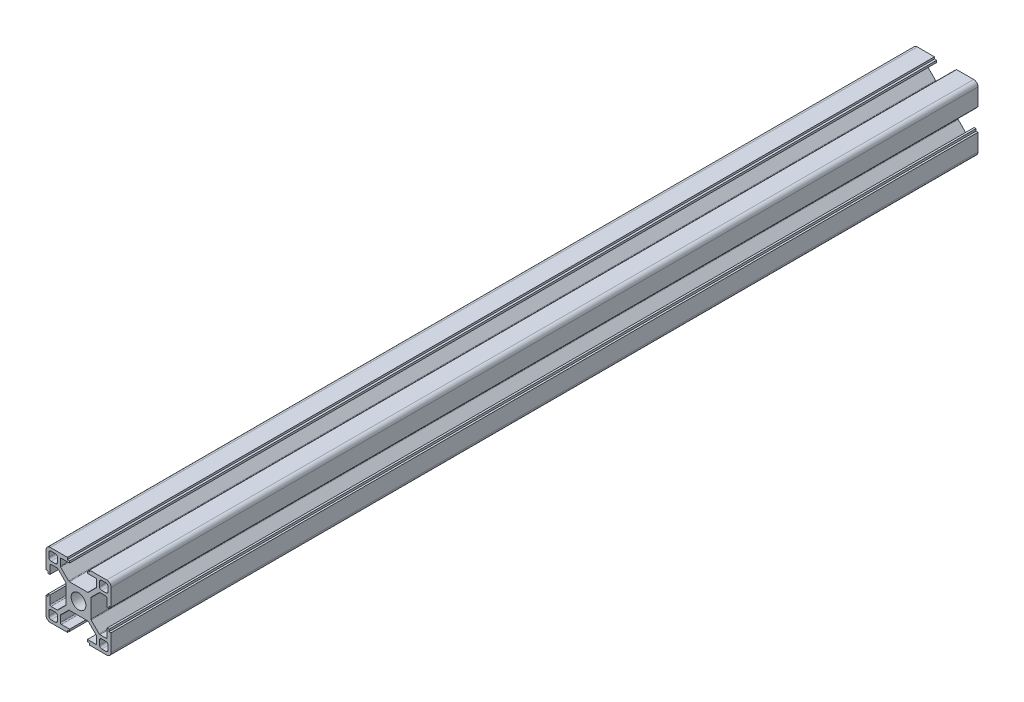
SolidWorks part; units mm, degrees
ref_plane "前视基准面" through (0, 0, 0) normal (0, 0, 1) x (1, 0, 0)
ref_plane "上视基准面" through (0, 0, 0) normal (0, 1, 0) x (1, 0, 0)
ref_plane "右视基准面" through (0, 0, 0) normal (1, 0, 0) x (0, 0, -1)
sketch "草图1" plane through (0, 0, 0) normal (0, 0, 1) x (1, 0, 0)
  line L0 (0, 0) -> (0, 65.3905) construction
  line L1 (0, 0) -> (64.2648, 0) construction
  line L2 (0, 0) -> (79.9729, 79.9729) construction
  line L3 (5.7, 0) -> (5.7, 4.4272)
  line L4 (5.7, 4.4272) -> (9.6728, 8.4)
  line L5 (9.6728, 8.4) -> (13.2, 8.4)
  line L6 (13.2, 8.4) -> (13.2, 4.1)
  line L7 (13.2, 4.1) -> (14.1, 4.1)
  line L8 (14.1, 4.1) -> (14.1, 5.1)
  line L9 (14.1, 5.1) -> (15, 5.1)
  line L10 (15, 5.1) -> (15, 15)
  line L11 (5.1, 15) -> (15, 15)
  line L12 (5.1, 14.1) -> (5.1, 15)
  line L13 (4.1, 14.1) -> (5.1, 14.1)
  line L14 (4.1, 13.2) -> (4.1, 14.1)
  line L15 (8.4, 13.2) -> (4.1, 13.2)
  line L16 (8.4, 9.6728) -> (8.4, 13.2)
  line L17 (4.4272, 5.7) -> (8.4, 9.6728)
  line L18 (0, 5.7) -> (4.4272, 5.7)
  line L20 (9.7, 9.7) -> (13.7, 9.7)
  line L21 (9.7, 9.7) -> (9.7, 13.7)
  line L22 (9.7, 13.7) -> (13.7, 13.7)
  line L23 (13.7, 9.7) -> (13.7, 13.7)
  line L24 (9.7, 9.7) -> (13.7, 13.7) construction
  line L25 (9.7, 13.7) -> (13.7, 9.7) construction
  line L26 (0, 5.7) -> (0, 0)
  line L27 (0, 0) -> (5.7, 0)
  point P9 (11.7, 11.7)
  dimension "D1" = 45
  dimension "D2" = 5.7
  dimension "D3" = 1.8
  dimension "D4" = 0.9
  dimension "D5" = 8.2
  dimension "D6" = 10.2
  dimension "D7" = 1.8
  dimension "D8" = 15
  dimension "D9" = 16.8
  dimension "D10" = 4
  dimension "D11" = 1.3
extrude "凸台-拉伸1" add sketch "草图1" along normal blind 400 contours L3 L4 L5 L6 L7 L8 L9 L10 L11 L12 L13 L14 L15 L16 L17 L18 L26 L27
fillet "圆角1" radius 1 4 edges at (9.7, 9.7, 200) (13.7, 9.7, 200) (9.7, 13.7, 200) (13.7, 13.7, 200)
fillet "圆角2" radius 2 1 edges at (15, 15, 200)
fillet "圆角3" radius 0.5 6 edges at (5.7, 4.4272, 200) (4.4272, 5.7, 200) (8.4, 13.2, 200) (8.4, 9.6728, 200) (9.6728, 8.4, 200) (13.2, 8.4, 200)
pattern_circular "阵列(圆周)1" count 4 over 360 about axis through (0, 0, 0) along (0, 0, 1) of "圆角2", "圆角3", "凸台-拉伸1", "圆角1"
sketch "草图2" plane through (0, 0, 400) normal (0, 0, 1) x (1, 0, 0)
  circle A0 centre (0, 0) radius 3.4
  dimension "D1" = 6.8
extrude "切除-拉伸1" cut sketch "草图2" against normal through all
sketch "草图3" plane through (0, 0, 0) normal (0, 1, 0) x (1, 0, 0)
  line L0 (-114.7373, -200) -> (117.0068, -200) construction
  line L1 (-4.2201, 0) -> (4.2201, 0) construction
  line L2 (4.2201, -400) -> (-4.2201, -400) construction
  line L3 (4.2201, 0) -> (-4.2201, 0) construction
  line L4 (0, 99.6796) -> (0, -462.0396) construction
  circle A0 centre (0, -200) radius 3.25
  circle A1 centre (0, -50) radius 3.25
  circle A2 centre (0, -350) radius 3.25
  dimension "D1" = 6.5
  dimension "D2" = 50
extrude "切除-拉伸2" cut sketch "草图3" against normal mid plane 20
sketch "草图5" plane through (0, 0, 0) normal (0, 1, 0) x (0, 0, -1)
  line L0 (-412.4454, 0) -> (17.2103, 0) construction
  line L1 (-200, 80.7637) -> (-200, -56.9608) construction
  line L10 (-400, 5.1) -> (-400, 13) construction
  line L11 (0, 5.1) -> (0, 13) construction
  circle A0 centre (-240, 0) radius 3.15
  circle A1 centre (-160, 0) radius 3.15
  dimension "D1" = 6.3
  dimension "D2" = 40
extrude "切除-拉伸3" cut sketch "草图5" against normal mid plane 30
sketch "草图6" plane through (5.7, 0, 0) normal (1, 0, 0) x (0, 0, -1)
  line L0 (-433.5267, 0) -> (57.7035, 0) construction
  line L1 (-200, 137.4459) -> (-200, -74.7061) construction
  line L2 (-400, 5.1) -> (-400, 13) construction
  line L3 (0, 5.1) -> (0, 13) construction
  circle A0 centre (-220, 0) radius 3.15
  circle A1 centre (-180, 0) radius 3.15
  dimension "D1" = 6.3
  dimension "D2" = 20
extrude "切除-拉伸4" cut sketch "草图6" against normal through all
